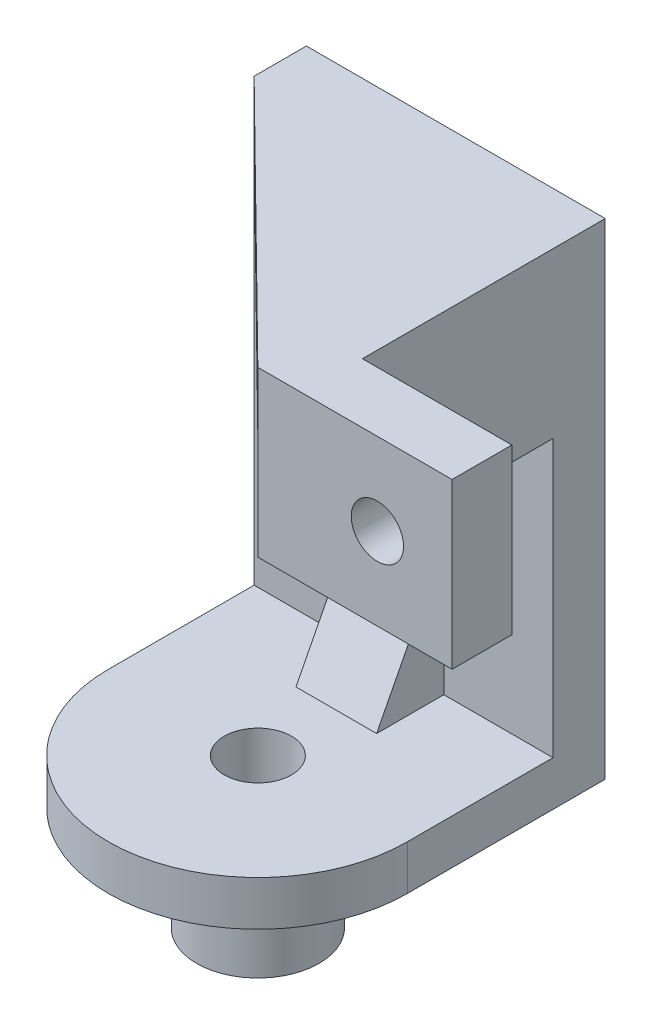
SolidWorks part; units mm, degrees
ref_plane "Alzado" through (0, 0, 0) normal (0, 0, 1) x (1, 0, 0)
ref_plane "Planta" through (0, 0, 0) normal (0, 1, 0) x (1, 0, 0)
ref_plane "Vista lateral" through (0, 0, 0) normal (1, 0, 0) x (0, 0, -1)
sketch "Croquis1" plane through (0, 0, 0) normal (0, 1, 0) x (1, 0, 0)
  line L0 (-18.716, 6.196) -> (1.284, 6.196) construction
  line L1 (-18.716, 19.446) -> (1.284, 19.446)
  line L2 (-18.716, 19.446) -> (-18.716, 6.196)
  line L4 (1.284, 19.446) -> (1.284, 6.196)
  arc A1 (1.284, 6.196) -> (-18.716, 6.196) centre (-8.716, 6.196) cw
  dimension "D1" = 20
  dimension "D2" = 13.25
extrude "Saliente-Extruir1" add sketch "Croquis1" along normal blind 3 contours L2 L0 L4 L1 | L0 A1
sketch "Croquis3" plane through (0, 3, 0) normal (0, 1, 0) x (1, 0, 0)
  line L0 (-8.716, 6.196) -> (-3.549, 6.196) construction
  circle A0 centre (-8.716, 6.196) radius 2.25
  dimension "D3" = 4.5
  dimension "D1" = 5.167
extrude "Cortar-Extruir1" cut sketch "Croquis3" against normal blind 3
sketch "Croquis7" plane through (0, 3, 0) normal (0, 1, 0) x (1, 0, 0)
  line L0 (-18.716, 19.446) -> (-18.716, 6.196) construction
  line L1 (1.284, 19.446) -> (-18.716, 19.446)
  line L2 (1.284, 19.446) -> (1.284, 15.946)
  line L3 (1.284, 15.946) -> (-18.716, 15.946)
  line L4 (-18.716, 19.446) -> (-18.716, 15.946)
  dimension "D1" = 3.5
extrude "Saliente-Extruir4" add sketch "Croquis7" along normal blind 25
sketch "Croquis6" plane through (0, 0, 0) normal (0, -1, 0) x (1, 0, 0)
  circle A0 centre (-8.716, -6.196) radius 4.1
  circle A1 centre (-8.716, -6.196) radius 2.25
  dimension "D1" = 8.2
extrude "Saliente-Extruir3" add sketch "Croquis6" along normal blind 7
sketch "Croquis8" plane through (0, 0, -19.446) normal (0, 0, -1) x (-1, 0, 0)
  line L0 (-1.284, 23) -> (18.716, 23) construction
  line L1 (-1.284, 28) -> (-1.284, 0) construction
  line L2 (18.716, 28) -> (18.716, 0) construction
  line L3 (-1.284, 28) -> (18.716, 28) construction
  circle A0 centre (8.716, 23) radius 2.25
  dimension "D2" = 4.5
  dimension "D1" = 5
extrude "Cortar-Extruir3" cut sketch "Croquis8" against normal blind 23
ref_plane "Plano4" through (0, -10, 0) normal (0, 1, 0) x (1, 0, 0)
ref_plane "Plano5" through (-8.716, 0, 0) normal (-1, 0, 0) x (0, 0, 1)
sketch "Croquis20" plane through (-8.716, 0, 0) normal (-1, 0, 0) x (0, 0, 1)
  line L0 (-15.946, 20.75) -> (-15.946, 11.75) construction
  line L1 (-8.446, 3) -> (-11.446, 3) construction
  line L4 (-15.946, 11.75) -> (-11.446, 3)
  dimension "D1" = 9
  dimension "D2" = 3
rib "Nervio6" sketch "Croquis20" sketch "Croquis20" thickness 5.4 extrusion direction parallel to sketch draft on no parameters "D1"=5.4
sketch "Croquis27" plane through (0, 0, -15.946) normal (0, 0, 1) x (1, 0, 0)
  line L0 (-8.716, 23) -> (-8.716, 27) construction
  line L1 (-8.716, 27) -> (6.284, 27) construction
  circle A0 centre (6.284, 27) radius 1.75
  dimension "D3" = 3.5
  dimension "D1" = 4
  dimension "D2" = 15
sketch "Croquis28" plane through (0, 0, -15.946) normal (0, 0, 1) x (1, 0, 0)
  line L0 (1.284, 28) -> (1.284, 32.5)
  line L1 (-18.716, 28) -> (-18.716, 32.5)
  line L2 (-18.716, 32.5) -> (1.284, 32.5)
  line L11 (-18.716, 3) -> (-11.416, 3)
  line L12 (-11.416, 3) -> (-11.416, 11.75)
  line L13 (-11.416, 11.75) -> (-6.016, 11.75)
  line L14 (-6.016, 11.75) -> (-6.016, 3)
  line L15 (-6.016, 3) -> (1.284, 3)
  line L16 (1.284, 3) -> (1.284, 28)
  line L17 (1.284, 28) -> (-18.716, 28)
  line L18 (-18.716, 28) -> (-18.716, 3)
  line L25 (1.284, 28) -> (-18.716, 28)
  dimension "D1" = 4.5
  dimension "D2" = 0
extrude "Saliente-Extruir6" add sketch "Croquis28" against normal blind 3.5
sketch "Croquis29" plane through (0, 0, -15.946) normal (0, 0, 1) x (1, 0, 0)
  line L1 (1.284, 32.5) -> (-1.716, 32.5)
  line L2 (1.284, 32.5) -> (1.284, 21.5)
  line L3 (1.284, 21.5) -> (-1.716, 21.5)
  line L4 (-1.716, 32.5) -> (-1.716, 21.5)
  dimension "D1" = 5.5
  dimension "D2" = 5.5
  dimension "D3" = 3
extrude "Saliente-Extruir7" add sketch "Croquis29" along normal blind 16.75
sketch "Croquis31" plane through (1.284, 0, 0) normal (1, 0, 0) x (0, 0, -1)
  line L0 (19.446, 32.5) -> (-0.804, 32.5) construction
  line L1 (-0.804, 21.5) -> (3.196, 21.5)
  line L2 (-0.804, 21.5) -> (-0.804, 32.5)
  line L3 (-0.804, 32.5) -> (3.196, 32.5)
  line L4 (3.196, 21.5) -> (3.196, 32.5)
  dimension "D1" = 4
extrude "Saliente-Extruir8" add sketch "Croquis31" along normal blind 10
extrude "Cortar-Extruir5" cut sketch "Croquis27" along normal blind 24 contours A0
ref_plane "Plano14" through (0, 32.5, 0) normal (0, 1, 0) x (1, 0, 0)
sketch "Croquis32" plane through (0, 32.5, 0) normal (0, 1, 0) x (1, 0, 0)
  line L0 (-1.716, -0.804) -> (-18.716, 15.946)
rib "Nervio7" sketch "Croquis32" sketch "Croquis32" thickness 4 extrusion direction parallel to sketch draft on no parameters "D1"=4
